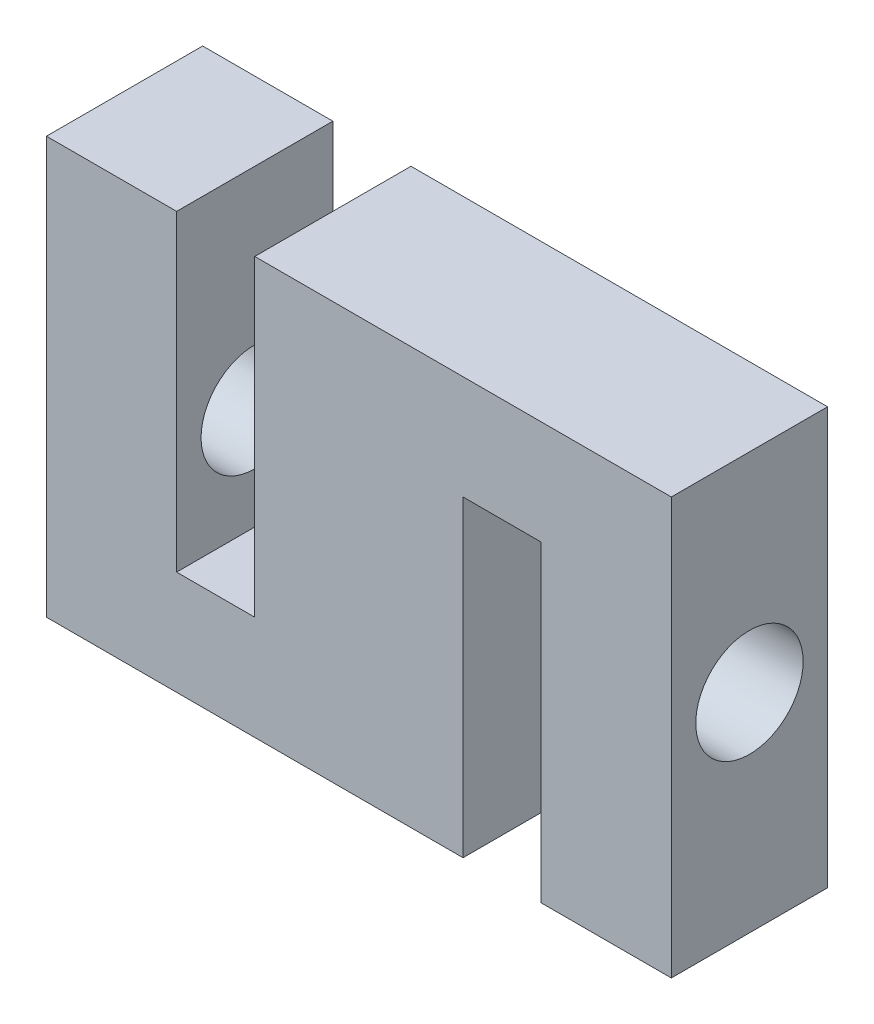
SolidWorks part; units mm, degrees
ref_plane "Front Plane" through (0, 0, 0) normal (0, 0, 1) x (1, 0, 0)
ref_plane "Top Plane" through (0, 0, 0) normal (0, 1, 0) x (1, 0, 0)
ref_plane "Right Plane" through (0, 0, 0) normal (1, 0, 0) x (0, 0, -1)
sketch "Sketch1" plane through (0, 0, 0) normal (0, 0, 1) x (1, 0, 0)
  line L0 (0, 0) -> (0, 50.8)
  line L1 (0, 50.8) -> (15.875, 50.8)
  line L2 (15.875, 50.8) -> (15.875, 12.7)
  line L3 (15.875, 12.7) -> (25.4, 12.7)
  line L4 (25.4, 12.7) -> (25.4, 50.8)
  line L5 (25.4, 50.8) -> (76.2, 50.8)
  line L6 (76.2, 50.8) -> (76.2, 0)
  line L7 (76.2, 0) -> (60.325, 0)
  line L8 (60.325, 0) -> (60.325, 38.1)
  line L9 (60.325, 38.1) -> (50.8, 38.1)
  line L10 (50.8, 38.1) -> (50.8, 0)
  line L11 (50.8, 0) -> (0, 0)
  dimension "D1" = 50.8
  dimension "D2" = 76.2
  dimension "D3" = 25.4
  dimension "D4" = 15.875
  dimension "D5" = 15.875
  dimension "D6" = 9.525
  dimension "D7" = 12.7
  dimension "D8" = 12.7
extrude "Boss-Extrude1" add sketch "Sketch1" along normal blind 19.05
hole_wizard "1/2 Clearance Hole1" positions "Sketch2" profile "Sketch4" hole size "1/2" standard "ANSI Inch" end condition up to next
sketch "Sketch2" plane through (0, 0, 0) normal (-1, 0, 0) x (0, 0, 1)
  line L0 (9.525, 25.4) -> (19.05, 25.4) construction
  line L1 (19.05, 50.8) -> (19.05, 0) construction
  line L3 (9.525, 0) -> (9.525, 25.4) construction
  line L4 (19.05, 0) -> (0, 0) construction
  point P0 (9.525, 25.4)
  point P15 (0, 0)
sketch "Sketch4" plane through (0, 25.4, 9.525) normal (0, 1, 0) x (0, 0, 1)
  line L0 (0, 0) -> (0, 15.875)
  line L1 (0, 15.875) -> (6.5481, 15.875)
  line L2 (6.5481, 15.875) -> (6.5481, 0)
  line L5 (6.5481, 0) -> (0, 0)
  line L11 (0, -6.35) -> (0, 107.95) construction
  dimension "Thru Hole Dia." = 13.0962
  dimension "Thru Hole Depth" = 15.875
hole_wizard "1/2 Clearance Hole2" positions "Sketch5" profile "Sketch6" hole size "1/2" standard "ANSI Inch" end condition up to next
sketch "Sketch5" plane through (76.2, 0, 0) normal (1, 0, 0) x (0, 0, -1)
  point P0 (-9.525, 25.4)
  point P3 (0, 0)
sketch "Sketch6" plane through (76.2, 25.4, 9.525) normal (0, 1, 0) x (0, 0, -1)
  line L0 (0, 0) -> (0, 15.875)
  line L1 (0, 15.875) -> (6.5481, 15.875)
  line L2 (6.5481, 15.875) -> (6.5481, 0)
  line L5 (6.5481, 0) -> (0, 0)
  line L11 (0, -6.35) -> (0, 107.95) construction
  dimension "Thru Hole Dia." = 13.0962
  dimension "Thru Hole Depth" = 15.875
